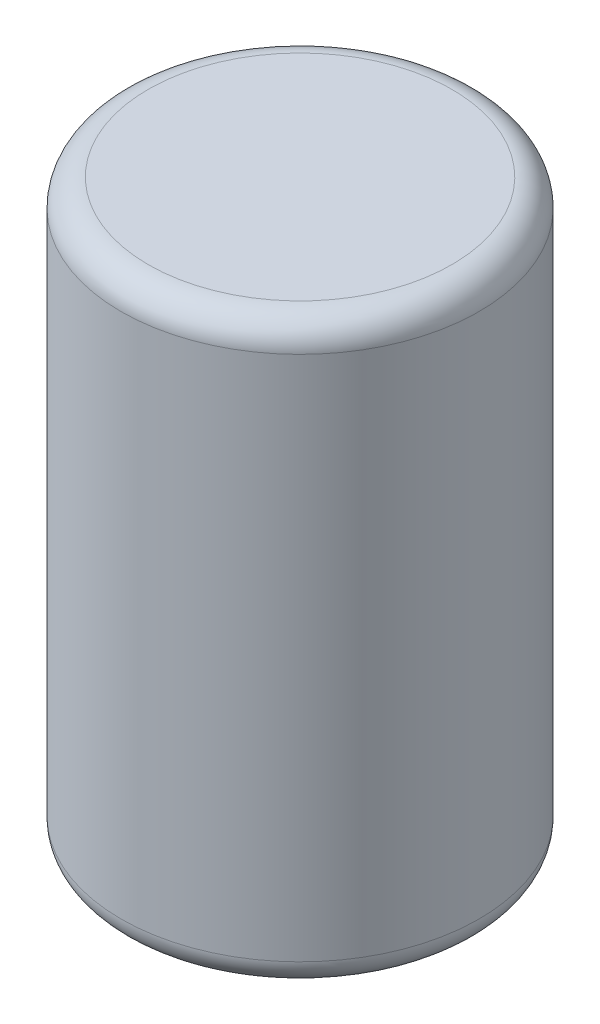
SolidWorks part; units mm, degrees
ref_plane "Front Plane" through (0, 0, 0) normal (0, 0, 1) x (1, 0, 0)
ref_plane "Top Plane" through (0, 0, 0) normal (0, 1, 0) x (1, 0, 0)
ref_plane "Right Plane" through (0, 0, 0) normal (1, 0, 0) x (0, 0, -1)
sketch "Sketch1" plane through (0, 0, 0) normal (0, 1, 0) x (1, 0, 0)
  circle A0 centre (0, 0) radius 6.6
  dimension "D1" = 13.2
extrude "Boss-Extrude1" add sketch "Sketch1" along normal blind 21.4
fillet "Fillet1" radius 1 2 edges at (0, 0, 6.6) (0, 21.4, 6.6)
sketch "Sketch2" plane through (0, 0, 0) normal (0, -1, 0) x (1, 0, 0)
  circle A0 centre (-2.5, 0) radius 0.3
  circle A1 centre (2.5, 0) radius 0.3
  point P4 (0, 0)
  dimension "D3" = 0.6
  dimension "D1" = 2.5
  dimension "D2" = 2.5
extrude "Boss-Extrude2" add sketch "Sketch2" along normal blind 2
